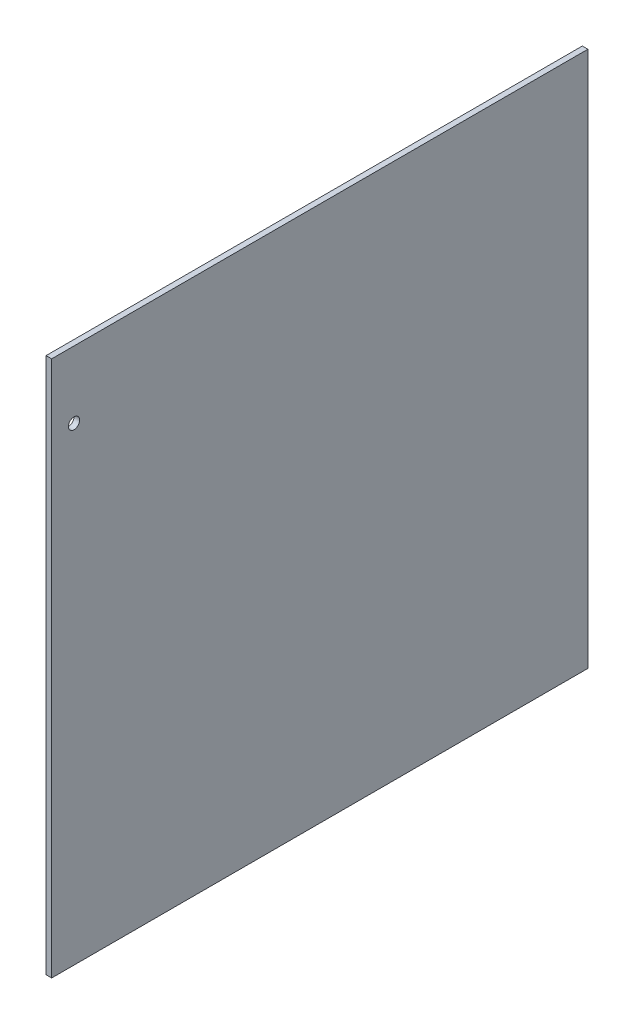
SolidWorks part; units mm, degrees
ref_plane "Front Plane" through (0, 0, 0) normal (0, 0, 1) x (1, 0, 0)
ref_plane "Top Plane" through (0, 0, 0) normal (0, 1, 0) x (1, 0, 0)
ref_plane "Right Plane" through (0, 0, 0) normal (1, 0, 0) x (0, 0, -1)
sketch "Sketch1" plane through (0, 0, 0) normal (1, 0, 0) x (0, 0, -1)
  line L1 (152.4, 152.4) -> (-152.4, 152.4)
  line L2 (152.4, 152.4) -> (152.4, -152.4)
  line L3 (152.4, -152.4) -> (-152.4, -152.4)
  line L4 (-152.4, 152.4) -> (-152.4, -152.4)
  line L5 (152.4, 152.4) -> (-152.4, -152.4) construction
  line L6 (152.4, -152.4) -> (-152.4, 152.4) construction
  point P0 (0, 0)
  dimension "D1" = 304.8
  dimension "D2" = 304.8
extrude "Boss-Extrude1" add sketch "Sketch1" along normal blind 3.175
sketch "Sketch2" plane through (0, 0, 0) normal (-1, 0, 0) x (0, 0, 1)
  line L1 (-152.4, 152.4) -> (152.4, 152.4) construction
  line L2 (152.4, 152.4) -> (152.4, -152.4) construction
  circle A0 centre (139.7, 114.3) radius 3.175
  dimension "D1" = 6.35
  dimension "D2" = 38.1
  dimension "D3" = 12.7
extrude "Cut-Extrude1" cut sketch "Sketch2" against normal through all
